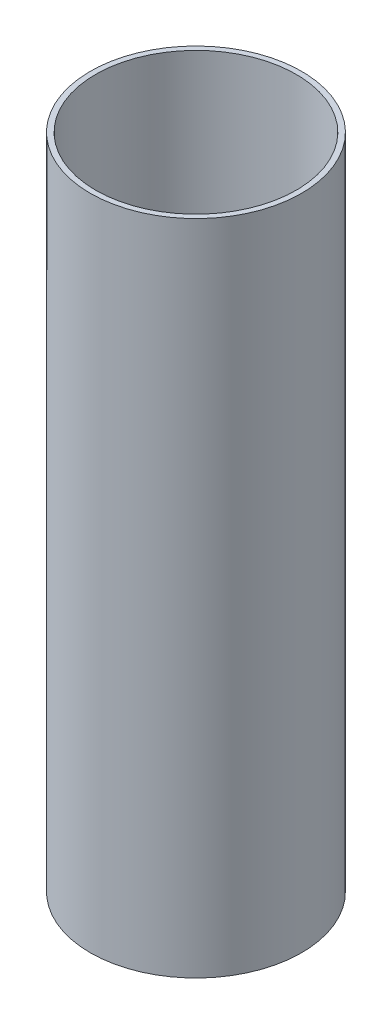
SolidWorks part; units mm, degrees
ref_plane "Front Plane" through (0, 0, 0) normal (0, 0, 1) x (1, 0, 0)
ref_plane "Top Plane" through (0, 0, 0) normal (0, 1, 0) x (1, 0, 0)
ref_plane "Right Plane" through (0, 0, 0) normal (1, 0, 0) x (0, 0, -1)
sketch "Sketch1" plane through (0, 0, 0) normal (0, 1, 0) x (1, 0, 0)
  circle A0 centre (0, 0) radius 30.5181
  circle A1 centre (0, 0) radius 32.1437
  dimension "D1" = 64.2874
  dimension "D2" = 61.0362
extrude "Boss-Extrude1" add sketch "Sketch1" along normal blind 200.025
